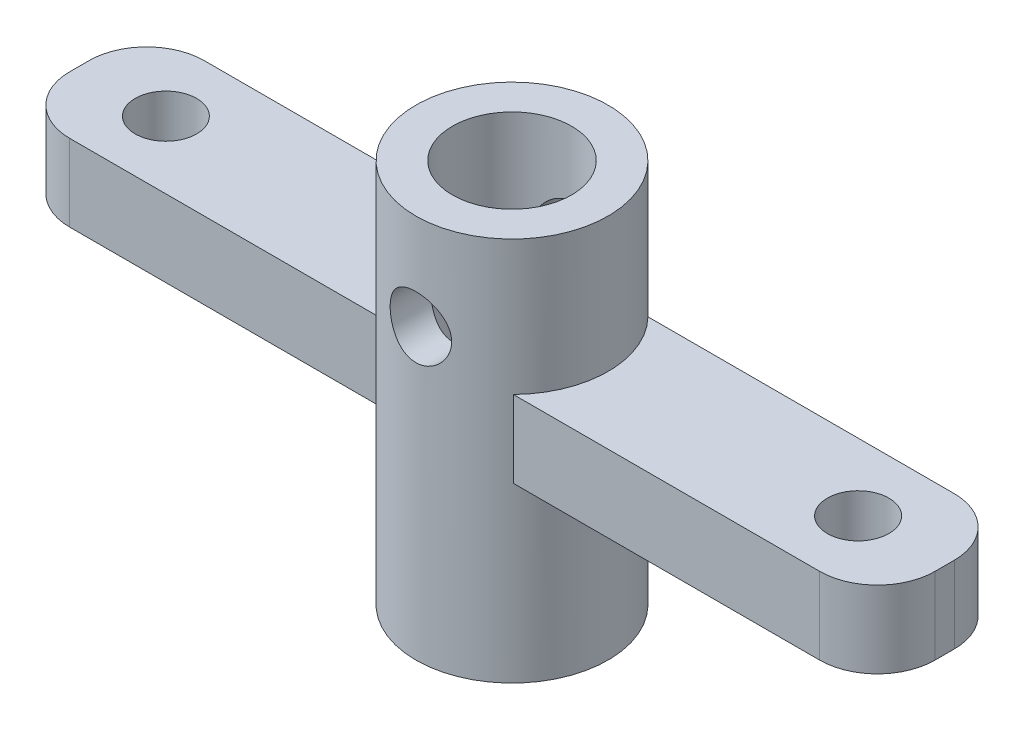
SolidWorks part; units mm, degrees
ref_plane "前视基准面" through (0, 0, 0) normal (0, 0, 1) x (1, 0, 0)
ref_plane "上视基准面" through (0, 0, 0) normal (0, 1, 0) x (1, 0, 0)
ref_plane "右视基准面" through (0, 0, 0) normal (1, 0, 0) x (0, 0, -1)
sketch "草图1" plane through (0, 0, 0) normal (0, 1, 0) x (1, 0, 0)
  circle A0 centre (0, 0) radius 3.1
  circle A1 centre (0, 0) radius 5
extrude "凸台-拉伸1" add sketch "草图1" along normal blind 20
sketch "草图2" plane through (0, 0, 0) normal (0, 0, 1) x (1, 0, 0)
  line L1 (22.5, 13) -> (-22.5, 13)
  line L2 (22.5, 13) -> (22.5, 9)
  line L3 (22.5, 9) -> (-22.5, 9)
  line L4 (-22.5, 13) -> (-22.5, 9)
  line L5 (22.5, 13) -> (-22.5, 9) construction
  line L6 (22.5, 9) -> (-22.5, 13) construction
  point P0 (0, 11)
extrude "凸台-拉伸2" add sketch "草图2" along normal mid plane 7
sketch "草图3" plane through (0, 13, 0) normal (0, 1, 0) x (1, 0, 0)
  circle A1 centre (0, 0) radius 3.1
sketch "草图4" plane through (0, 13, 0) normal (0, 1, 0) x (1, 0, 0)
  circle A0 centre (-18, 0) radius 1.6
  circle A1 centre (18, 0) radius 1.6
extrude "切除-拉伸2" cut sketch "草图4" against normal through all
fillet "圆角1" radius 3 4 edges at (22.5, 11, -3.5) (22.5, 11, 3.5) (-22.5, 11, -3.5) (-22.5, 11, 3.5)
sketch "草图5" plane through (0, 0, 0) normal (0, 0, 1) x (1, 0, 0)
  circle A0 centre (0, 15) radius 1.6
extrude "切除-拉伸3" cut sketch "草图5" against normal through all both and the other way through all
extrude "切除-拉伸4" cut sketch "草图3" against normal through all both and the other way through all contours A1
